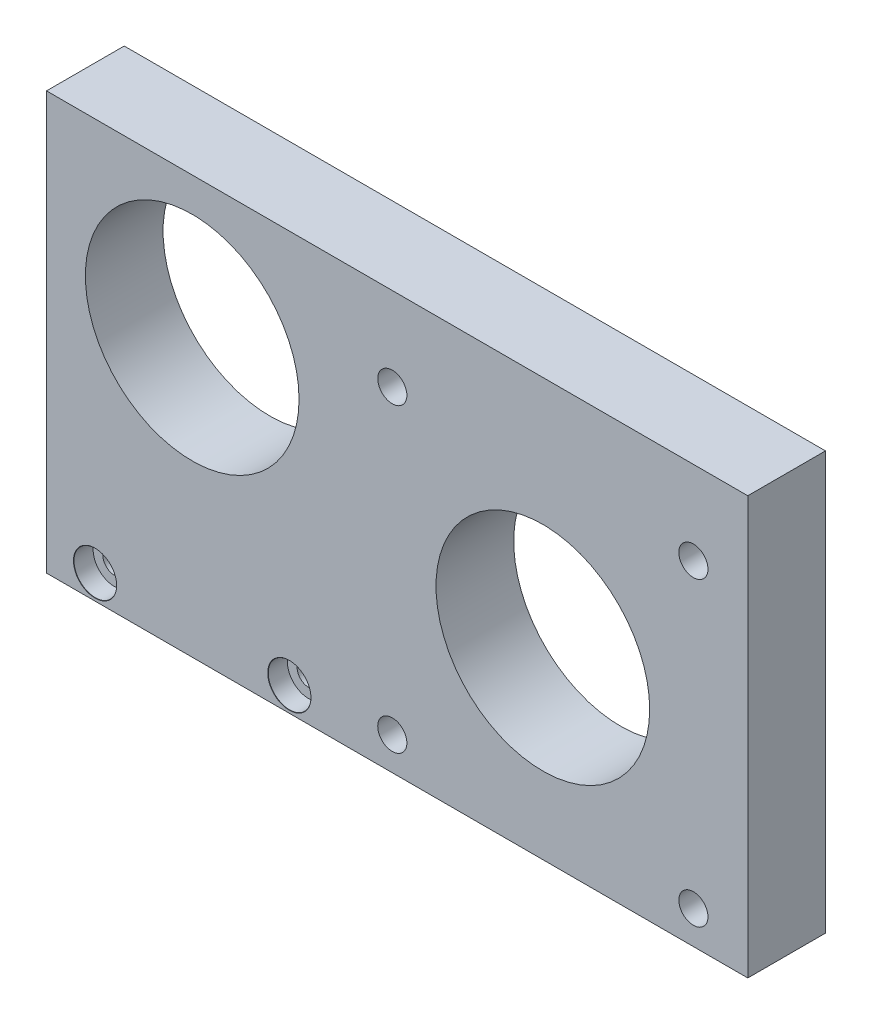
SolidWorks part; units mm, degrees
material "Liga 6061"
ref_plane "Plano frontal" through (0, 0, 0) normal (0, 0, 1) x (1, 0, 0)
ref_plane "Plano superior" through (0, 0, 0) normal (0, 1, 0) x (1, 0, 0)
ref_plane "Plano direito" through (0, 0, 0) normal (1, 0, 0) x (0, 0, -1)
sketch "Esboço1" plane through (0, 0, 0) normal (0, 0, 1) x (1, 0, 0)
  line L1 (36.1, -21.5) -> (-36.1, -21.5)
  line L2 (36.1, -21.5) -> (36.1, 21.5)
  line L3 (36.1, 21.5) -> (-36.1, 21.5)
  line L4 (-36.1, -21.5) -> (-36.1, 21.5)
  line L5 (36.1, -21.5) -> (-36.1, 21.5) construction
  line L6 (36.1, 21.5) -> (-36.1, -21.5) construction
  point P0 (0, 0)
  dimension "D1" = 43
  dimension "D2" = 72.2
extrude "Ressalto-extrusão1" add sketch "Esboço1" along normal blind 8
sketch "Esboço2" plane through (0, 0, 8) normal (0, 0, 1) x (1, 0, 0)
  line L0 (-36.1, -21.5) -> (36.1, -21.5) construction
  line L1 (-36.1, 21.5) -> (-36.1, -21.5) construction
  line L2 (36.1, -21.5) -> (36.1, 21.5) construction
  line L3 (15, -24.5188) -> (15, 27.7556) construction
  line L4 (-9.9532, -2.6) -> (54.4593, -2.6) construction
  circle A0 centre (-21.1, 7) radius 11
  circle A1 centre (15, -2.6) radius 11
  circle A2 centre (-0.5, 12.9) radius 1.5
  circle A3 centre (30.5, 12.9) radius 1.5
  circle A4 centre (30.5, -18.1) radius 1.5
  circle A5 centre (-0.5, -18.1) radius 1.5
  dimension "D1" = 22
  dimension "D2" = 28.5
  dimension "D3" = 15
  dimension "D4" = 22
  dimension "D6" = 21.1
  dimension "D7" = 3
  dimension "D8" = 15.5
  dimension "D9" = 15.5
  dimension "D5" = 18.9
extrude "Corte-extrusão1" cut sketch "Esboço2" against normal through all
hole_wizard "Rebaixo para SHCS M21" positions "Esboço5" profile "Esboço6" counterbore size "M2" standard "Ansi Metric" end condition through all
sketch "Esboço5" plane through (0, 0, 8) normal (0, 0, 1) x (1, 0, 0)
  line L0 (-36.1, -21.5) -> (36.1, -21.5) construction
  line L1 (-36.1, 21.5) -> (-36.1, -21.5) construction
  point P0 (-31.1, -19)
  point P2 (-11.1, -19)
  dimension "D1" = 2.5
  dimension "D2" = 5
  dimension "D3" = 2.5
  dimension "D4" = 20
sketch "Esboço6" plane through (-31.1, -19, 8) normal (1, 0, 0) x (0, -1, 0)
  line L0 (0, 0) -> (0, 8)
  line L1 (0, 8) -> (1.2, 8)
  line L3 (1.2, 8) -> (1.2, 2)
  line L4 (2.2, 2) -> (1.2, 2)
  line L5 (2.2, 2) -> (2.2, 0.025)
  line L6 (2.2, 0.025) -> (2.225, 0)
  line L7 (2.225, 0) -> (0, 0)
  line L8 (-2.2, 0.025) -> (-2.225, 0) construction
  line L11 (0, -6.35) -> (0, 107.95) construction
  dimension "Thru Hole Dia." = 2.4
  dimension "Thru Hole Depth" = 8
  dimension "C'Bore Dia." = 4.4
  dimension "C'Bore Depth" = 2
  dimension "Near C'Sink Dia." = 4.45
  dimension "Near C'Sink Angle" = 90
